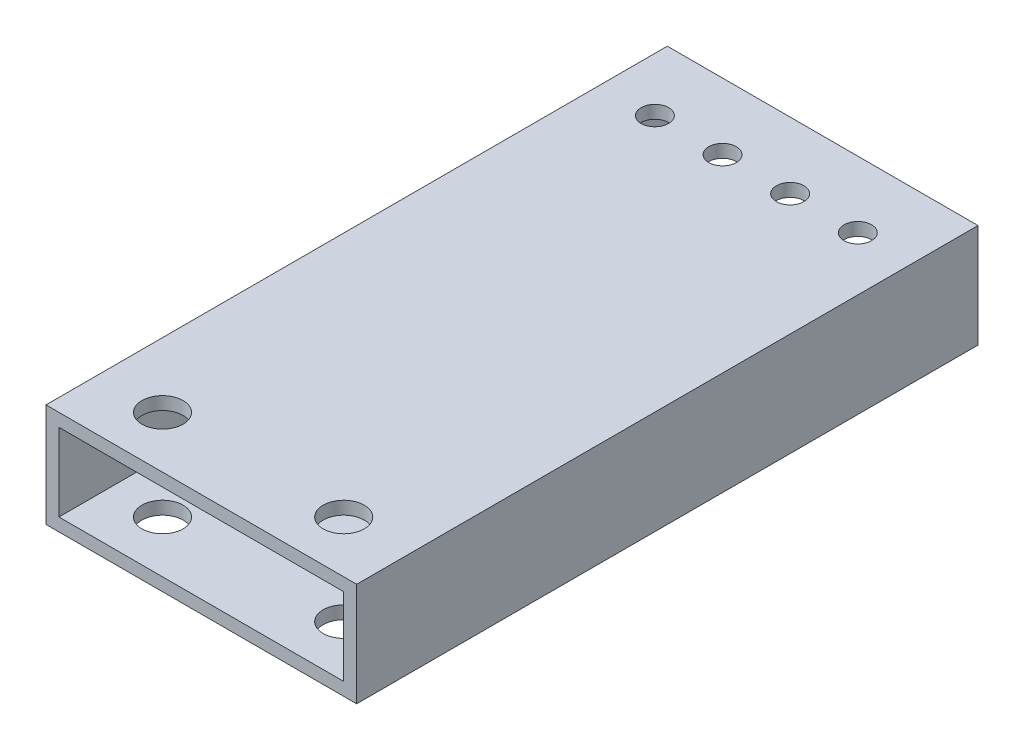
SolidWorks part; units mm, degrees
material "6061-T6 (SS)"
ref_plane "Front Plane" through (0, 0, 0) normal (0, 0, 1) x (1, 0, 0)
ref_plane "Top Plane" through (0, 0, 0) normal (0, 1, 0) x (1, 0, 0)
ref_plane "Right Plane" through (0, 0, 0) normal (1, 0, 0) x (0, 0, -1)
sketch "Sketch1" plane through (0, 0, 0) normal (0, 0, 1) x (1, 0, 0)
  line L0 (3.175, 22.225) -> (73.025, 22.225)
  line L1 (0, 0) -> (76.2, 0)
  line L2 (0, 0) -> (0, 25.4)
  line L3 (0, 25.4) -> (76.2, 25.4)
  line L4 (76.2, 0) -> (76.2, 25.4)
  line L5 (73.025, 3.175) -> (73.025, 22.225)
  line L6 (3.175, 3.175) -> (73.025, 3.175)
  line L7 (3.175, 3.175) -> (3.175, 22.225)
  dimension "D1" = 76.2
  dimension "D2" = 25.4
  dimension "D3" = 3.175
extrude "Boss-Extrude1" add sketch "Sketch1" along normal blind 152.4
sketch "Sketch2" plane through (0, 25.4, 0) normal (0, 1, 0) x (1, 0, 0)
  circle A0 centre (13.2131, -16.2687) radius 3.3782
  circle A1 centre (29.8044, -16.2687) radius 3.3782
  circle A2 centre (46.3956, -16.2687) radius 3.3782
  circle A3 centre (62.9869, -16.2687) radius 3.3782
  dimension "D1" = 6.7564
  dimension "D2" = 6.7564
  dimension "D3" = 6.7564
  dimension "D4" = 6.7564
extrude "Cut-Extrude1" cut sketch "Sketch2" against normal through all
sketch "Sketch3" plane through (0, 0, 0) normal (0, -1, 0) x (1, 0, 0)
  line L0 (0, 152.4) -> (76.2, 152.4) construction
  line L1 (0, 152.4) -> (0, 0) construction
  line L2 (76.2, 152.4) -> (76.2, 0) construction
  circle A0 centre (60.325, 139.7) radius 5.0419
  circle A1 centre (15.875, 139.7) radius 5.0419
  dimension "D1" = 10.0838
  dimension "D2" = 10.0838
  dimension "D3" = 44.45
  dimension "D4" = 12.7
  dimension "D5" = 15.875
  dimension "D6" = 15.875
extrude "Cut-Extrude2" cut sketch "Sketch3" against normal through all
